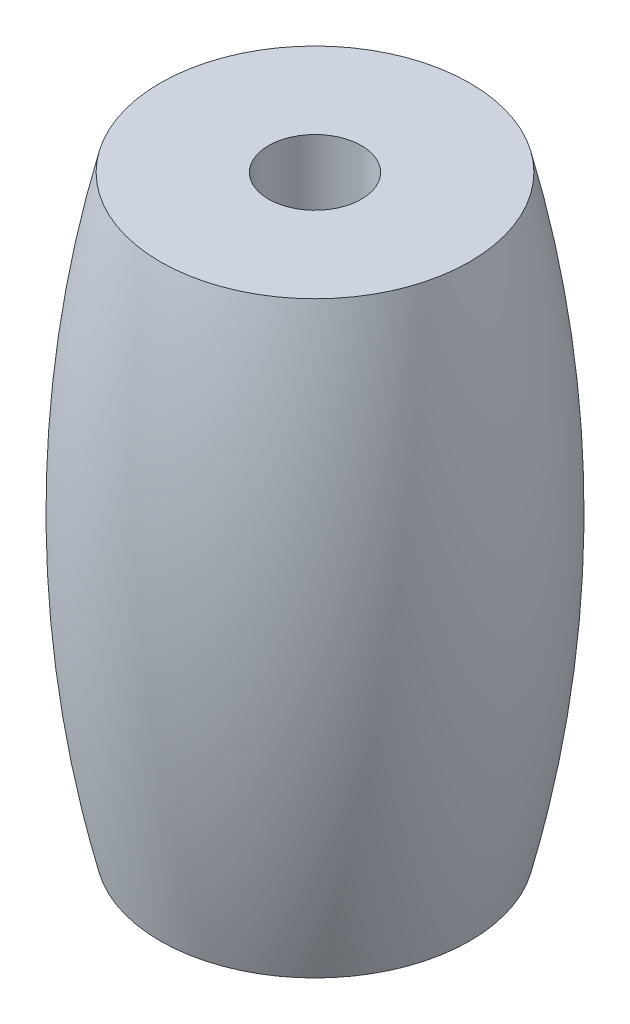
SolidWorks part; units mm, degrees
material "BUTYL"
ref_plane "前视基准面" through (0, 0, 0) normal (0, 0, 1) x (1, 0, 0)
ref_plane "上视基准面" through (0, 0, 0) normal (0, 1, 0) x (1, 0, 0)
ref_plane "右视基准面" through (0, 0, 0) normal (1, 0, 0) x (0, 0, -1)
other "Configuration Table"
sketch "草图1" plane through (0, 0, 0) normal (0, 0, 1) x (1, 0, 0)
  line L0 (-1.5, 14.8255) -> (-1.5, -4.1745)
  line L1 (-1.5, -4.1745) -> (-5, -4.1745)
  line L2 (-1.5, 14.8255) -> (-5, 14.8255)
  line L3 (0, 17.0979) -> (0, -6.6783) construction
  arc A0 (-5, 14.8255) -> (-5, -4.1745) centre (33.8555, 5.3255) ccw
  dimension "D5" = 40
  dimension "D1" = 1.5
  dimension "D2" = 19
  dimension "D3" = 3.5
  dimension "D4" = 3.5
revolve "旋转1" add sketch "草图1" angle 360 about L3
